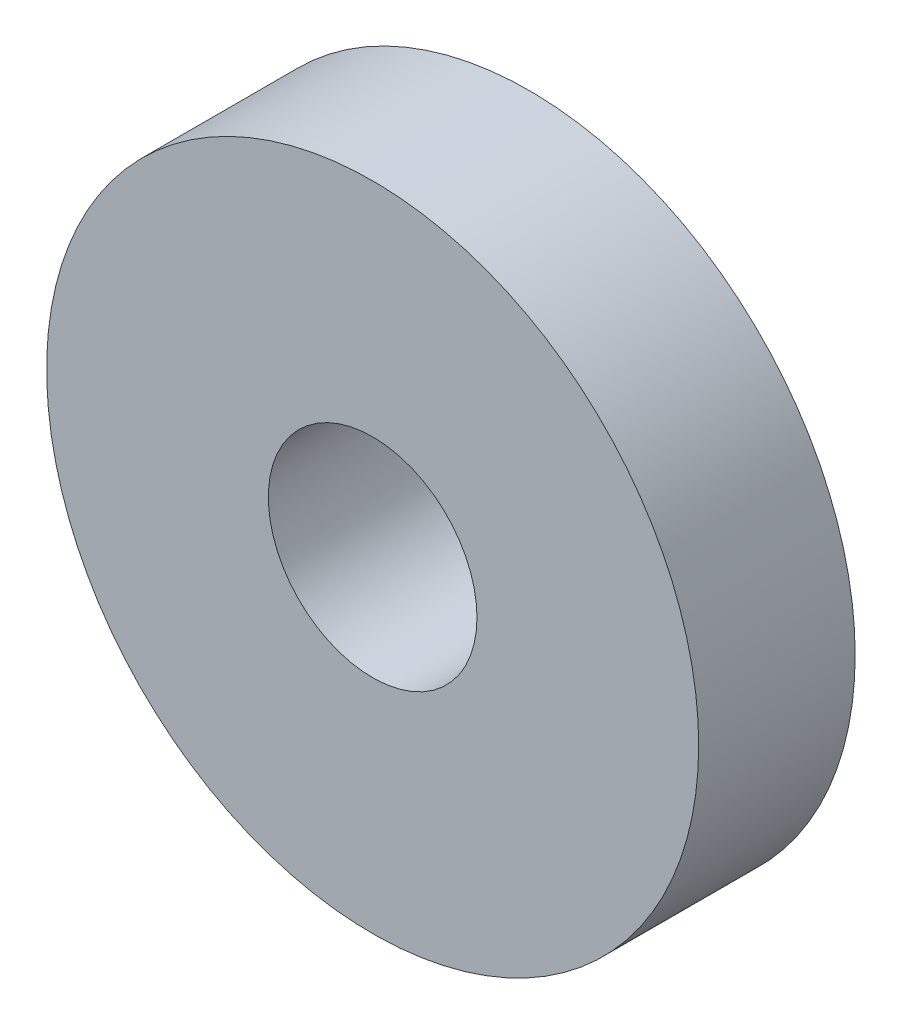
SolidWorks part; units mm, degrees
other "Markup1"
sketch "Sketch2" plane through (25, 25, 10) normal (0.6714, 0.4492, 0.5895) x (0.72, -0.2069, -0.6624)
ref_plane "Front Plane" through (0, 0, 0) normal (0, 0, 1) x (1, 0, 0)
ref_plane "Top Plane" through (0, 0, 0) normal (0, 1, 0) x (1, 0, 0)
ref_plane "Right Plane" through (0, 0, 0) normal (1, 0, 0) x (0, 0, -1)
sketch "Sketch1" plane through (0, 0, 0) normal (0, 0, 1) x (1, 0, 0)
  circle A0 centre (0, 0) radius 25
  circle A1 centre (0, 0) radius 8
  dimension "D1" = 50
  dimension "D2" = 16
extrude "Boss-Extrude1" add sketch "Sketch1" along normal blind 12
